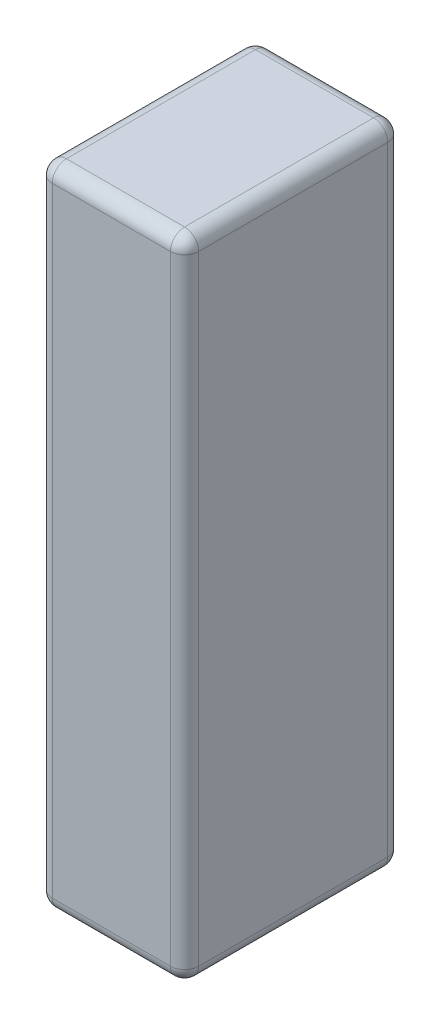
SolidWorks part; units mm, degrees
material "Lipo 5S"
ref_plane "Front Plane" through (0, 0, 0) normal (0, 0, 1) x (1, 0, 0)
ref_plane "Top Plane" through (0, 0, 0) normal (0, 1, 0) x (1, 0, 0)
ref_plane "Right Plane" through (0, 0, 0) normal (1, 0, 0) x (0, 0, -1)
sketch "Sketch1" plane through (0, 0, 0) normal (0, 1, 0) x (1, 0, 0)
  line L1 (0, 0) -> (31, 0)
  line L2 (0, 0) -> (0, 46)
  line L3 (0, 46) -> (31, 46)
  line L4 (31, 0) -> (31, 46)
  dimension "D1" = 46
  dimension "D2" = 31
extrude "Boss-Extrude1" add sketch "Sketch1" along normal blind 137
fillet "Fillet1" radius 3 12 edges at (15.5, 137, -46) (15.5, 0, -46) (0, 68.5, -46) (0, 137, -23) (0, 0, -23) (31, 137, -23) (31, 68.5, -46) (31, 0, -23) (0, 68.5, 0) (15.5, 137, 0) (31, 68.5, 0) (15.5, 0, 0)
